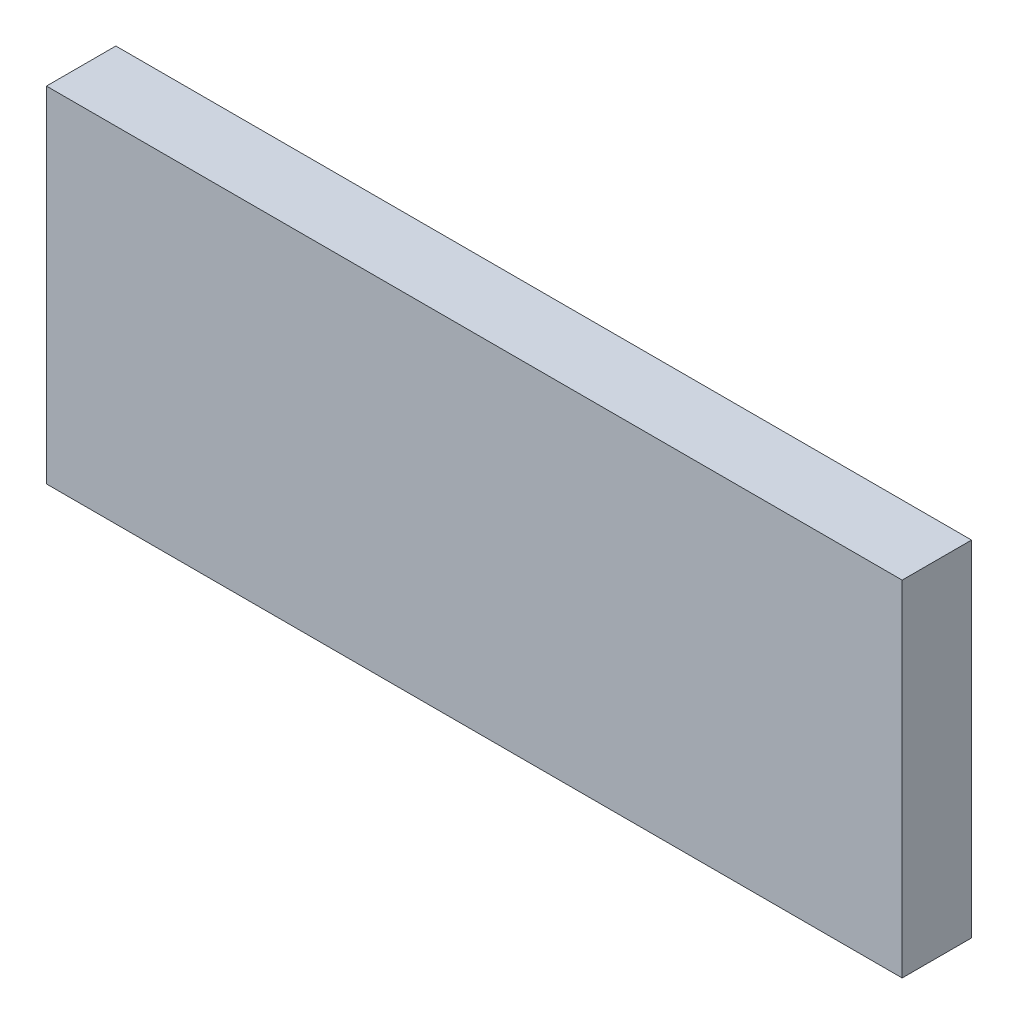
SolidWorks part; units mm, degrees
ref_plane "Front Plane" through (0, 0, 0) normal (0, 0, 1) x (1, 0, 0)
ref_plane "Top Plane" through (0, 0, 0) normal (0, 1, 0) x (1, 0, 0)
ref_plane "Right Plane" through (0, 0, 0) normal (1, 0, 0) x (0, 0, -1)
sketch "Sketch1" plane through (0, 0, 0) normal (0, 0, 1) x (1, 0, 0)
  line L1 (-24.5, 6) -> (12.5, 6)
  line L2 (-24.5, 6) -> (-24.5, -8.9)
  line L3 (-24.5, -8.9) -> (12.5, -8.9)
  line L4 (12.5, 6) -> (12.5, -8.9)
  dimension "D1" = 37
  dimension "D2" = 14.9
extrude "Boss-Extrude1" add sketch "Sketch1" along normal blind 3
